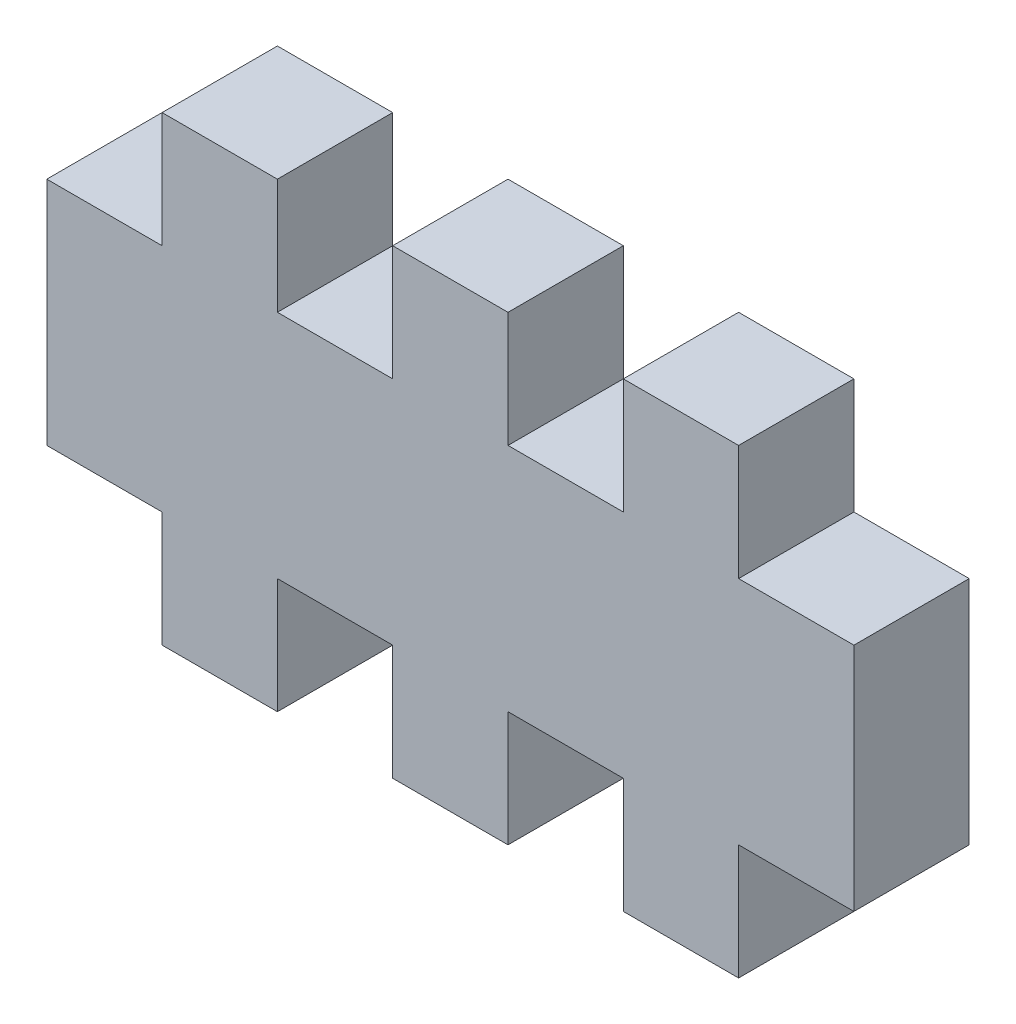
SolidWorks part; units mm, degrees
ref_plane "Plan de face" through (0, 0, 0) normal (0, 0, 1) x (1, 0, 0)
ref_plane "Plan de dessus" through (0, 0, 0) normal (0, 1, 0) x (1, 0, 0)
ref_plane "Plan de droite" through (0, 0, 0) normal (1, 0, 0) x (0, 0, -1)
sketch "Esquisse1" plane through (0, 0, 0) normal (0, 0, 1) x (1, 0, 0)
  line L0 (12, 6) -> (12, 9)
  line L1 (0, 0) -> (21, 0)
  line L2 (0, 0) -> (0, 6)
  line L3 (0, 6) -> (21, 6)
  line L4 (21, 0) -> (21, 6)
  line L5 (3, 6) -> (6, 6)
  line L6 (3, 6) -> (3, 9)
  line L7 (3, 9) -> (6, 9)
  line L8 (6, 6) -> (6, 9)
  line L9 (9, 9) -> (12, 9)
  line L10 (9, 6) -> (9, 9)
  line L11 (18, 6) -> (18, 9)
  line L12 (15, 9) -> (18, 9)
  line L13 (15, 6) -> (15, 9)
  line L14 (0, 3) -> (21, 3) construction
  line L15 (18, 0) -> (18, -3)
  line L16 (15, -3) -> (18, -3)
  line L17 (15, 0) -> (15, -3)
  line L18 (12, 0) -> (12, -3)
  line L19 (9, -3) -> (12, -3)
  line L20 (9, 0) -> (9, -3)
  line L21 (6, 0) -> (6, -3)
  line L22 (3, -3) -> (6, -3)
  line L23 (3, 0) -> (3, -3)
  dimension "D1" = 6
  dimension "D2" = 21
  dimension "D3" = 3
  dimension "D4" = 3
  dimension "D5" = 3
  dimension "D6" = 3
extrude "Boss.-Extru.1" add sketch "Esquisse1" along normal blind 3 contours L1 L23 L22 L21 | L1 L20 L19 L18 | L1 L17 L16 L15 | L14 L2 L1 L4 | L2 L14 L4 L3 | L3 L8 L7 L6 | L10 L3 L0 L9 | L13 L3 L11 L12
